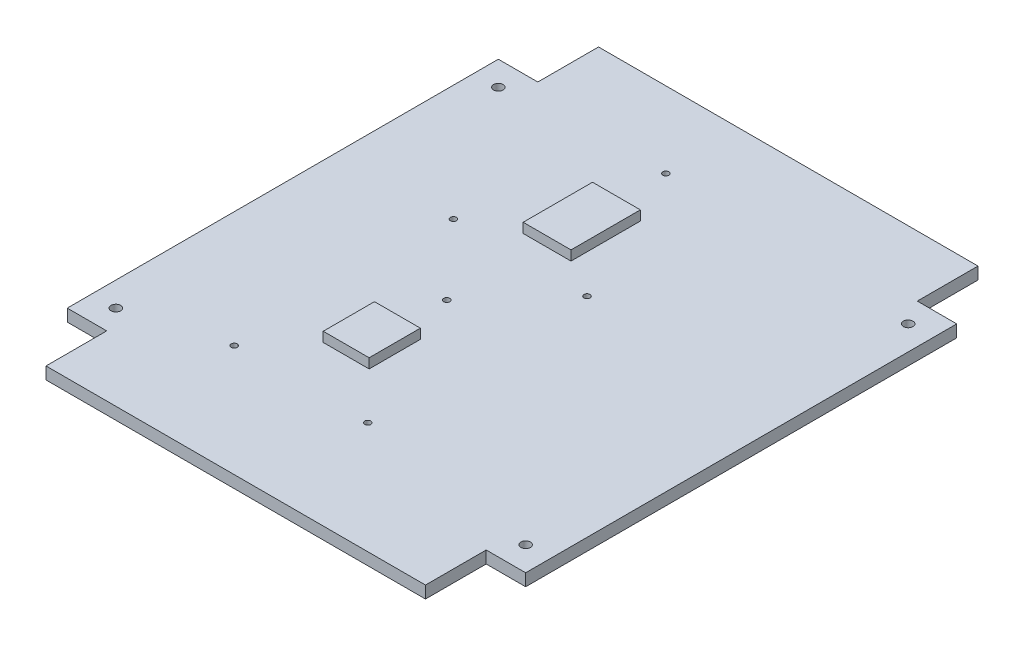
SolidWorks part; units mm, degrees
ref_plane "Front Plane" through (0, 0, 0) normal (0, 0, 1) x (1, 0, 0)
ref_plane "Top Plane" through (0, 0, 0) normal (0, 1, 0) x (1, 0, 0)
ref_plane "Right Plane" through (0, 0, 0) normal (1, 0, 0) x (0, 0, -1)
sketch "Sketch1" plane through (0, 0, 0) normal (0, 1, 0) x (1, 0, 0)
  line L0 (-47.9425, 45.085) -> (-39.6875, 45.085)
  line L1 (39.6875, -57.785) -> (-39.6875, -57.785)
  line L2 (47.9425, -45.085) -> (47.9425, 45.085)
  line L3 (39.6875, 57.785) -> (-39.6875, 57.785)
  line L4 (-47.9425, -45.085) -> (-47.9425, 45.085)
  line L5 (47.9425, -57.785) -> (-47.9425, 57.785) construction
  line L6 (47.9425, 57.785) -> (-47.9425, -57.785) construction
  line L7 (-39.6875, 45.085) -> (-39.6875, 57.785)
  line L8 (0, 0) -> (0, 88.612) construction
  line L9 (47.9425, 45.085) -> (39.6875, 45.085)
  line L10 (39.6875, 45.085) -> (39.6875, 57.785)
  line L11 (0, 0) -> (102.5577, 0) construction
  line L12 (39.6875, -45.085) -> (39.6875, -57.785)
  line L13 (47.9425, -45.085) -> (39.6875, -45.085)
  line L14 (-47.9425, -45.085) -> (-39.6875, -45.085)
  line L15 (-39.6875, -45.085) -> (-39.6875, -57.785)
  point P0 (0, 0)
  dimension "D1" = 115.57
  dimension "D2" = 95.885
  dimension "D3" = 8.255
  dimension "D4" = 12.7
extrude "Boss-Extrude1" add sketch "Sketch1" along normal blind 2.54
sketch "Sketch3" plane through (0, 0, 0) normal (0, 1, 0) x (1, 0, 0)
  line L0 (47.9425, -45.085) -> (47.9425, 45.085) construction
  line L1 (-14.9479, -24.5364) -> (-5.3467, -24.5364)
  line L2 (-14.9479, -24.5364) -> (-14.9479, -13.8176)
  line L3 (-14.9479, -13.8176) -> (-5.3467, -13.8176)
  line L4 (-5.3467, -24.5364) -> (-5.3467, -13.8176)
  line L5 (-14.9479, -24.5364) -> (-5.3467, -13.8176) construction
  line L6 (-14.9479, -13.8176) -> (-5.3467, -24.5364) construction
  line L7 (-39.6875, -57.785) -> (39.6875, -57.785) construction
  line L9 (-3.7719, 16.1163) -> (-13.7795, 16.1163)
  line L10 (-3.7719, 16.1163) -> (-3.7719, 30.6197)
  line L11 (-3.7719, 30.6197) -> (-13.7795, 30.6197)
  line L12 (-13.7795, 16.1163) -> (-13.7795, 30.6197)
  line L13 (-3.7719, 16.1163) -> (-13.7795, 30.6197) construction
  line L14 (-3.7719, 30.6197) -> (-13.7795, 16.1163) construction
  point P0 (-10.1473, -19.177)
  point P9 (-8.7757, 23.368)
  dimension "D1" = 58.0898
  dimension "D2" = 38.608
  dimension "D3" = 10.7188
  dimension "D4" = 9.6012
  dimension "D5" = 56.7182
  dimension "D6" = 81.153
  dimension "D7" = 10.0076
  dimension "D8" = 14.5034
extrude "Boss-Extrude2" add sketch "Sketch3" along normal blind 4.572
sketch "Sketch4" plane through (0, 2.54, 0) normal (0, 1, 0) x (1, 0, 0)
  line L0 (-39.6875, -57.785) -> (39.6875, -57.785) construction
  line L1 (47.9425, -45.085) -> (47.9425, 45.085) construction
  circle A0 centre (4.2545, -34.417) radius 0.635
  circle A1 centre (-23.6855, -34.417) radius 0.635
  circle A2 centre (-9.7155, -3.937) radius 0.635
  circle A3 centre (4.2545, 11.43) radius 0.635
  circle A4 centre (-23.6855, 11.43) radius 0.635
  circle A5 centre (-9.7155, 41.91) radius 0.635
  dimension "D8" = 1.27
  dimension "D9" = 1.27
  dimension "D10" = 1.27
  dimension "D11" = 1.27
  dimension "D12" = 1.27
  dimension "D13" = 1.27
  dimension "D1" = 23.368
  dimension "D2" = 43.688
  dimension "D3" = 71.628
  dimension "D4" = 53.848
  dimension "D5" = 57.658
  dimension "D6" = 69.215
  dimension "D7" = 99.695
extrude "Cut-Extrude1" cut sketch "Sketch4" against normal through all
sketch "Sketch5" plane through (0, 2.54, 0) normal (0, 1, 0) x (1, 0, 0)
  line L0 (-39.6875, -57.785) -> (39.6875, -57.785) construction
  line L1 (47.9425, -45.085) -> (47.9425, 45.085) construction
  circle A0 centre (42.8625, -40.005) radius 0.9995
  circle A1 centre (42.8625, 40.005) radius 0.9995
  circle A2 centre (-42.8625, -40.005) radius 0.9995
  circle A3 centre (-42.8625, 40.005) radius 0.9995
  dimension "D3" = 1.999
  dimension "D6" = 1.999
  dimension "D7" = 1.999
  dimension "D8" = 1.999
  dimension "D1" = 17.78
  dimension "D2" = 5.08
  dimension "D4" = 97.79
  dimension "D5" = 90.805
extrude "Cut-Extrude2" cut sketch "Sketch5" against normal through all
equation "\"Heat Sink Holes\"= .05"
equation "\"D10@Sketch4\"=\"Heat Sink Holes\""
equation "\"D11@Sketch4\"=\"Heat Sink Holes\""
equation "\"D12@Sketch4\"=\"Heat Sink Holes\""
equation "\"D13@Sketch4\"=\"Heat Sink Holes\""
equation "\"D9@Sketch4\"=\"Heat Sink Holes\""
equation "\"D8@Sketch4\"=\"Heat Sink Holes\""
equation "\"Mounting Holes\"= .0787"
equation "\"D3@Sketch5\"=\"Mounting Holes\""
equation "\"D6@Sketch5\"=\"Mounting Holes\""
equation "\"D7@Sketch5\"=\"Mounting Holes\""
equation "\"D8@Sketch5\"=\"Mounting Holes\""
